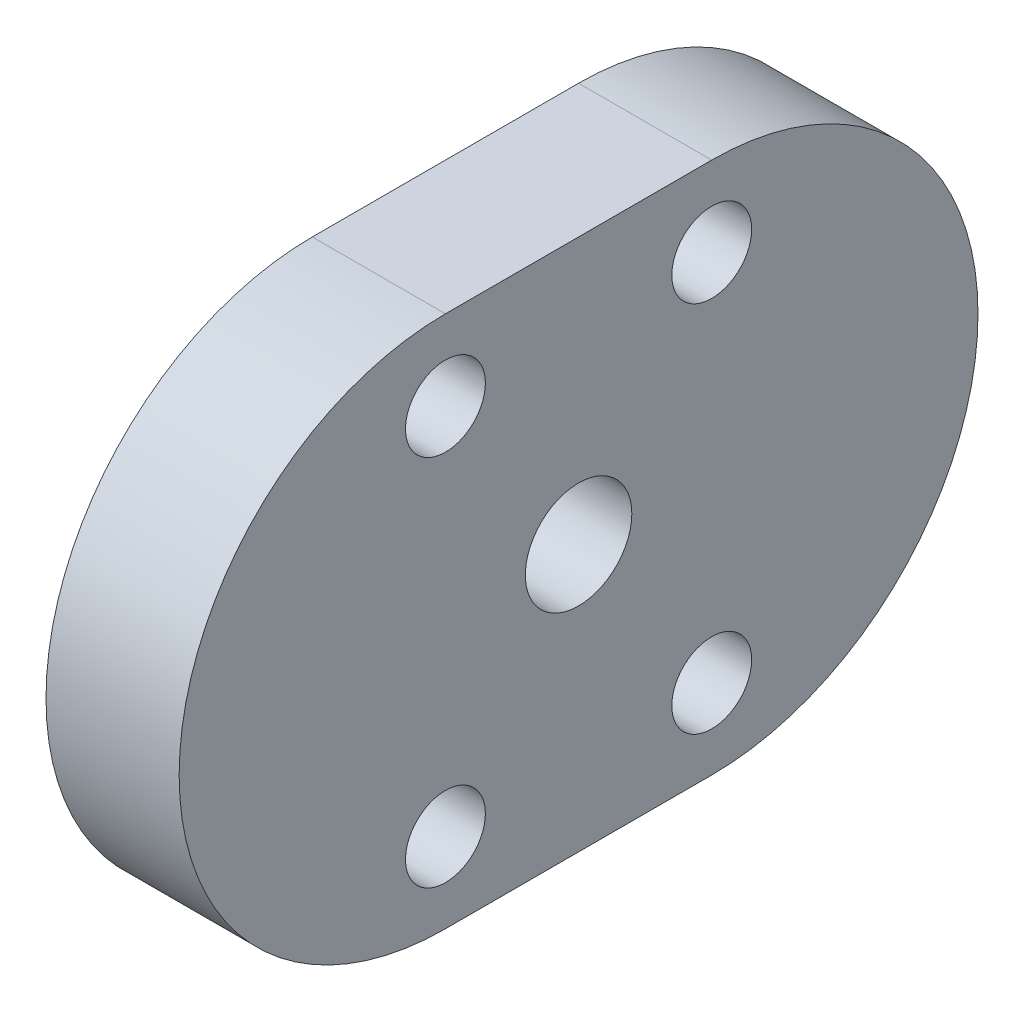
SolidWorks part; units mm, degrees
material "PMMA"
ref_plane "Front Plane" through (0, 0, 0) normal (0, 0, 1) x (1, 0, 0)
ref_plane "Top Plane" through (0, 0, 0) normal (0, 1, 0) x (1, 0, 0)
ref_plane "Right Plane" through (0, 0, 0) normal (1, 0, 0) x (0, 0, -1)
sketch "Schizzo1" plane through (0, 0, 0) normal (1, 0, 0) x (0, 0, -1)
  line L0 (-5, 10) -> (5, 10)
  line L1 (-5, -10) -> (5, -10)
  line L2 (-5, 10) -> (5, -10) construction
  arc A0 (-5, 10) -> (-5, -10) centre (-5, 0) ccw
  arc A1 (5, 10) -> (5, -10) centre (5, 0) cw
  point P4 (0, 0)
  dimension "D1" = 10
  dimension "D2" = 10
  dimension "D3" = 20
extrude "Estrusione-Estrusione1" add sketch "Schizzo1" along normal blind 5
sketch "Schizzo2" plane through (0, 0, 0) normal (1, 0, 0) x (0, 0, -1)
  line L0 (-5, 0) -> (5, 0) construction
  line L1 (-5, 10) -> (-5, -10) construction
  line L2 (5, 10) -> (5, -10) construction
  circle A0 centre (-5, 7) radius 1.5
  circle A1 centre (0, 0) radius 2
  circle A2 centre (5, 7) radius 1.5
  circle A3 centre (-5, -7) radius 1.5
  circle A4 centre (5, -7) radius 1.5
  dimension "D1" = 3
  dimension "D3" = 4
  dimension "D2" = 7
  dimension "D4" = 7
  dimension "D5" = 7
  dimension "D6" = 7
extrude "Taglio-Estrusione1" cut sketch "Schizzo2" along direction (1, 0, 0) on the side of the normal through all
equation "\"Thick5\"=5"
equation "\"D1@Estrusione-Estrusione1\"=\"Thick5\""
equation "\"D4@Schizzo2\"=\"D2@Schizzo2\""
equation "\"D5@Schizzo2\"=\"D4@Schizzo2\""
equation "\"D6@Schizzo2\"=\"D2@Schizzo2\""
